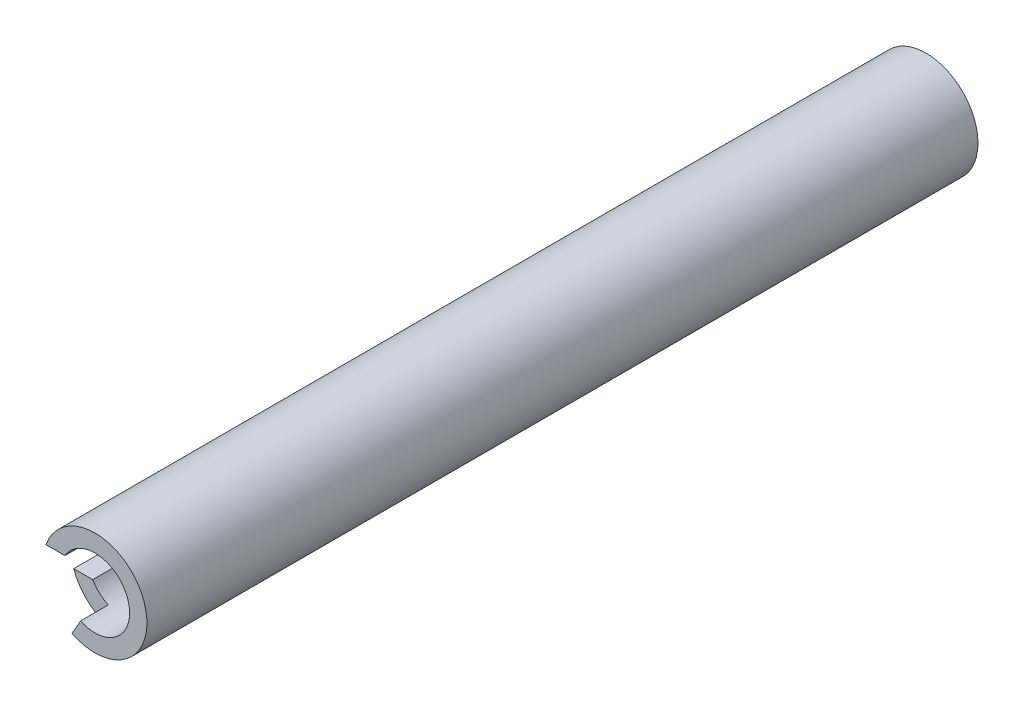
SolidWorks part; units mm, degrees
ref_plane "Front Plane" through (0, 0, 0) normal (0, 0, 1) x (1, 0, 0)
ref_plane "Top Plane" through (0, 0, 0) normal (0, 1, 0) x (1, 0, 0)
ref_plane "Right Plane" through (0, 0, 0) normal (1, 0, 0) x (0, 0, -1)
sketch "Sketch1" plane through (0, 0, 0) normal (0, 0, 1) x (1, 0, 0)
  circle A0 centre (0, 0) radius 19.05
extrude "Boss-Extrude1" add sketch "Sketch1" along normal blind 304.8 contours A0
sketch "Sketch3" plane through (0, 0, 304.8) normal (0, 0, 1) x (1, 0, 0)
  circle A0 centre (0, 0) radius 12.7
extrude "Cut-Extrude1" cut sketch "Sketch3" against normal blind 273.05
sketch "Sketch4" plane through (0, 0, 0) normal (0, 0, -1) x (-1, 0, 0)
  circle A0 centre (0, 0) radius 2.54
extrude "Cut-Extrude2" cut sketch "Sketch4" against normal blind 31.75
ref_plane "Plane1" through (0, 0, 307.34) normal (0, 0, 1) x (1, 0, 0)
sketch "Sketch5" plane through (0, 0, 307.34) normal (0, 0, 1) x (1, 0, 0)
  line L2 (-12.7, 6.35) -> (-8.7101, 6.35)
  line L3 (-8.7101, 6.35) -> (-8.7101, -6.35)
  line L4 (-8.7101, -6.35) -> (-20.268, -6.35)
  line L5 (-20.268, -6.35) -> (-20.268, 6.35)
  line L6 (-20.268, 6.35) -> (-12.7, 6.35)
extrude "Cut-Extrude3" cut sketch "Sketch5" against normal blind 273.05
sketch "Sketch7" plane through (0, 0, 307.34) normal (0, 0, 1) x (1, 0, 0)
  line L0 (-17.9605, -6.35) -> (-18.1776, -12.6963)
  line L3 (-8.3077, -6.35) -> (-17.9605, -6.35)
  line L7 (-18.1776, -17.4897) -> (-18.1776, -12.6963)
  line L9 (-4.2333, -9.6622) -> (-8.3077, -6.35)
  line L10 (-4.2333, -9.6622) -> (-8.6655, -17.4897)
  line L11 (-8.6655, -17.4897) -> (-18.1776, -17.4897)
extrude "Cut-Extrude4" cut sketch "Sketch7" against normal blind 12.7
